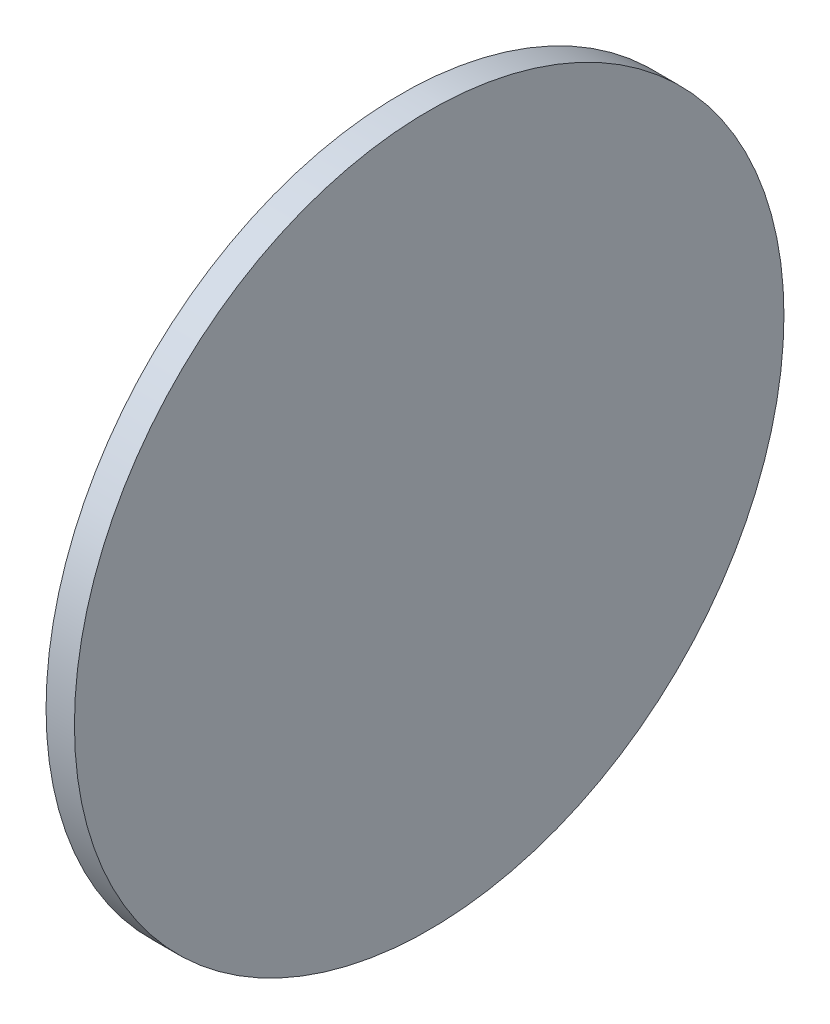
SolidWorks part; units mm, degrees
ref_plane "前视基准面" through (0, 0, 0) normal (0, 0, 1) x (1, 0, 0)
ref_plane "上视基准面" through (0, 0, 0) normal (0, 1, 0) x (1, 0, 0)
ref_plane "右视基准面" through (0, 0, 0) normal (1, 0, 0) x (0, 0, -1)
sketch "草图1" plane through (0, 0, 0) normal (0, 0, 1) x (1, 0, 0)
  line L0 (0, 25) -> (0, 0)
  line L2 (0, 25) -> (2, 25)
  line L3 (0, 0) -> (2, 0)
  line L4 (2, 25) -> (2, 0)
  dimension "D1" = 25
  dimension "D2" = 2
revolve "旋转2" add sketch "草图1" angle 360 about L3
